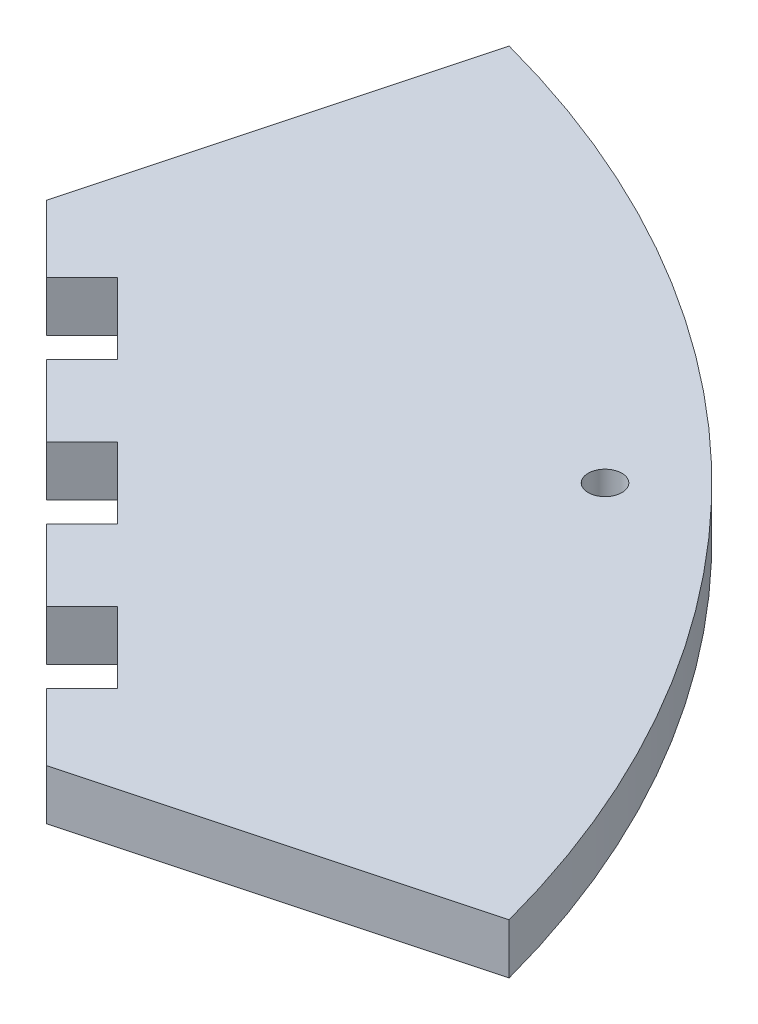
SolidWorks part; units mm, degrees
ref_plane "Front Plane" through (0, 0, 0) normal (0, 0, 1) x (1, 0, 0)
ref_plane "Top Plane" through (0, 0, 0) normal (0, 1, 0) x (1, 0, 0)
ref_plane "Right Plane" through (0, 0, 0) normal (1, 0, 0) x (0, 0, -1)
sketch "Sketch1" plane through (0, 0, 0) normal (0, 1, 0) x (1, 0, 0)
  line L0 (69.85, 0) -> (107.95, 0)
  line L1 (0, 69.85) -> (0, 107.95)
  line L2 (0, 69.85) -> (0, 0) construction
  line L3 (0, 0) -> (69.85, 0) construction
  line L4 (27.9395, 104.2717) -> (18.0785, 67.4699)
  line L5 (67.4699, 18.0785) -> (104.2717, 27.9395)
  line L6 (18.0785, 67.4699) -> (67.4699, 18.0785)
  line L7 (0, 69.85) -> (18.0785, 67.4699) construction
  line L8 (67.4699, 18.0785) -> (69.85, 0) construction
  arc A0 (107.95, 0) -> (0, 107.95) centre (0, 0) ccw
  arc A1 (0, 69.85) -> (69.85, 0) centre (0, 0) cw
  dimension "D3" = 60
  dimension "D1" = 38.1
  dimension "D2" = 107.95
extrude "Boss-Extrude1" add sketch "Sketch1" along normal blind 5.08 contours L4 A1 L5 A0 | A1 L6
sketch "Sketch2" plane through (0, 5.08, 0) normal (0, 1, 0) x (1, 0, 0)
  line L0 (18.0785, 67.4699) -> (67.4699, 18.0785) construction
  line L1 (18.0785, 67.4699) -> (67.4699, 18.0785) construction
  line L2 (42.7742, 42.7742) -> (76.3322, 76.3322) construction
  arc A0 (104.2717, 27.9395) -> (27.9395, 104.2717) centre (0, 0) ccw construction
  arc A1 (104.2717, 27.9395) -> (27.9395, 104.2717) centre (0, 0) ccw construction
  point P7 (70.944, 70.944)
  dimension "D1" = 7.62
hole_wizard "M3 Clearance Hole1" positions "Sketch3" profile "Sketch4" hole size "M3" standard "ANSI Metric"
sketch "Sketch3" plane through (0, 5.08, 0) normal (0, 1, 0) x (1, 0, 0)
  point P0 (70.944, 70.944)
sketch "Sketch4" plane through (70.944, 5.08, -70.944) normal (1, 0, 0) x (0, 0, 1)
  line L0 (0, 0) -> (0, 12.9595)
  line L1 (0, 12.9595) -> (1.7, 11.938)
  line L2 (1.7, 11.938) -> (1.7, 0)
  line L5 (1.7, 0) -> (0, 0)
  line L10 (0, 12.9595) -> (-1.7, 11.938) construction
  line L11 (0, -6.35) -> (0, 107.95) construction
  dimension "Hole Dia." = 3.4
  dimension "Hole Depth" = 11.938
  dimension "Drill Angle" = 118
sketch "Sketch5" plane through (0, 5.08, 0) normal (0, 1, 0) x (1, 0, 0)
  line L0 (64.3268, 28.4058) -> (57.1426, 35.59) construction
  line L1 (57.1426, 35.59) -> (53.5505, 31.9979) construction
  line L2 (53.5505, 31.9979) -> (60.7347, 24.8137) construction
  line L3 (60.7347, 24.8137) -> (64.3268, 28.4058) construction
  line L4 (49.9584, 42.7742) -> (42.7742, 49.9584) construction
  line L5 (42.7742, 49.9584) -> (39.1821, 46.3663) construction
  line L6 (39.1821, 46.3663) -> (46.3663, 39.1821) construction
  line L7 (46.3663, 39.1821) -> (49.9584, 42.7742) construction
  line L8 (24.8137, 60.7347) -> (31.9979, 53.5505) construction
  line L9 (31.9979, 53.5505) -> (35.59, 57.1426) construction
  line L10 (35.59, 57.1426) -> (28.4058, 64.3268) construction
  line L11 (28.4058, 64.3268) -> (24.8137, 60.7347) construction
  line L12 (64.3268, 28.4058) -> (57.1426, 35.59)
  line L13 (57.1426, 35.59) -> (53.5505, 31.9979)
  line L14 (53.5505, 31.9979) -> (60.7347, 24.8137)
  line L15 (60.7347, 24.8137) -> (64.3268, 28.4058)
  line L16 (49.9584, 42.7742) -> (42.7742, 49.9584)
  line L17 (42.7742, 49.9584) -> (39.1821, 46.3663)
  line L18 (39.1821, 46.3663) -> (46.3663, 39.1821)
  line L19 (46.3663, 39.1821) -> (49.9584, 42.7742)
  line L20 (24.8137, 60.7347) -> (31.9979, 53.5505)
  line L21 (31.9979, 53.5505) -> (35.59, 57.1426)
  line L22 (35.59, 57.1426) -> (28.4058, 64.3268)
  line L23 (28.4058, 64.3268) -> (24.8137, 60.7347)
extrude "Cut-Extrude1" cut sketch "Sketch5" against normal up to next
equation "\"Foamcore\"= 0.2in"
equation "\"MDF\"= 0.2in"
equation "\"D1@Boss-Extrude1\"=\"MDF\""
